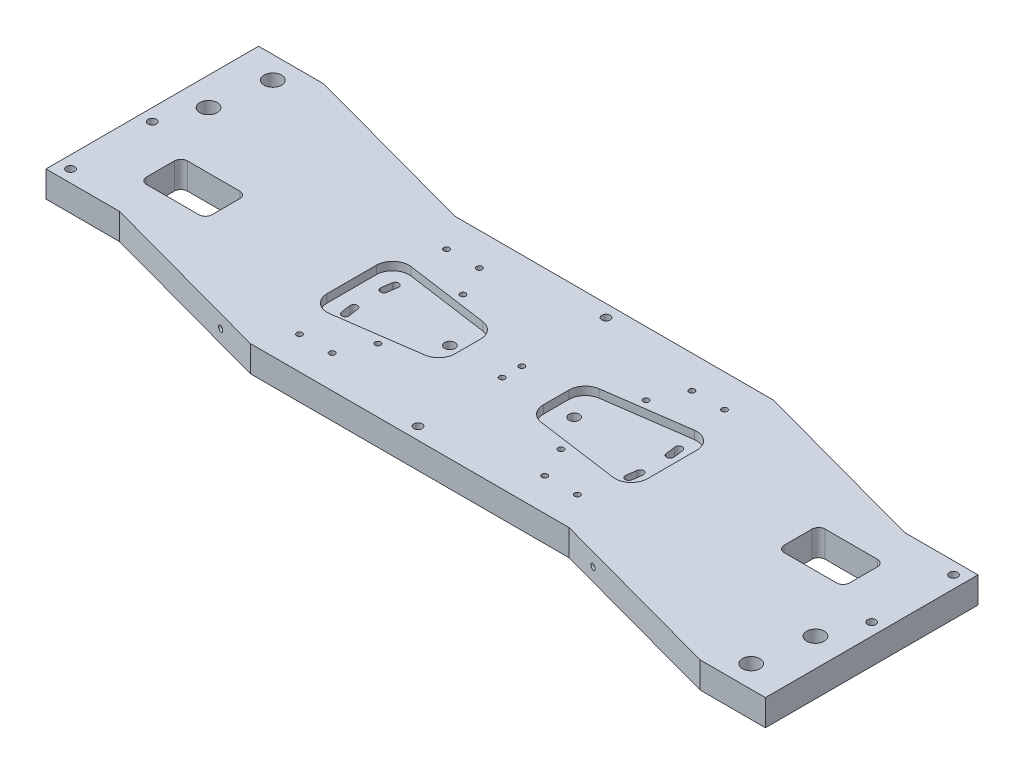
SolidWorks part; units mm, degrees
ref_plane "Front" through (0, 0, 0) normal (0, 0, 1) x (1, 0, 0)
ref_plane "Top" through (0, 0, 0) normal (0, 1, 0) x (1, 0, 0)
ref_plane "Right" through (0, 0, 0) normal (1, 0, 0) x (0, 0, -1)
sketch "Sketch1" plane through (0, 0, 0) normal (0, 0, 1) x (1, 0, 0)
  line L0 (0, 40.7324) -> (0, -22.0561) construction
  line L2 (250, 0) -> (250, -16)
  line L3 (-250, 0) -> (250, 0)
  line L4 (-250, 0) -> (-250, -16)
  line L5 (-250, -16) -> (250, -16)
  dimension "D1" = 16
  dimension "D2" = 500
  dimension "D3" = 250
extrude "Base-Extrude" add sketch "Sketch1" along normal mid plane 130
sketch "Sketch3" plane through (0, 0, 0) normal (0, 1, 0) x (-1, 0, 0)
  line L0 (-250, -65) -> (250, -65) construction
  line L1 (-210, 95) -> (-100, 65)
  line L2 (-250, 65) -> (-250, 95)
  line L3 (-250, 95) -> (-210, 95)
  line L4 (-100, 65) -> (-250, 65)
  line L5 (210, -95) -> (100, -65)
  line L6 (250, -65) -> (250, -95)
  line L7 (250, -95) -> (210, -95)
  line L8 (100, -65) -> (250, -65)
  line L9 (-250, 65) -> (250, 65) construction
  dimension "D1" = 160
  dimension "D2" = 40
  dimension "D3" = 40
  dimension "D4" = 160
  dimension "D5" = 110
  dimension "D6" = 110
extrude "Extrusion for Blade Clamping" add sketch "Sketch3" against normal up to surface (16 mm away) up to face at (0, -16, 0)
sketch "Sketch4" plane through (0, 0, 0) normal (0, 1, 0) x (-1, 0, 0)
  line L0 (-210, 95) -> (-250, 95) construction
  line L1 (-205, -35) -> (-95, -65)
  line L2 (250, 65) -> (250, 35)
  line L3 (250, 35) -> (205, 35)
  line L4 (205, 35) -> (95, 65)
  line L6 (-250, -65) -> (-250, -35)
  line L7 (-250, -35) -> (-205, -35)
  line L8 (-250, -65) -> (100, -65) construction
  line L9 (210, -95) -> (250, -95) construction
  line L10 (-100, 65) -> (250, 65) construction
  line L11 (95, 65) -> (250, 65)
  line L12 (-95, -65) -> (-250, -65)
  dimension "D1" = 130
  dimension "D2" = 45
  dimension "D3" = 130
  dimension "D4" = 45
  dimension "D5" = 110
  dimension "D6" = 110
extrude "Cutaway to Balance Blade Extrusion" cut sketch "Sketch4" against normal up to surface (16 mm away)
sketch "Sketch5" plane through (0, 0, 0) normal (0, 1, 0) x (-1, 0, 0)
  line L0 (273.4836, 0) -> (-275.6627, 0) construction
  line L1 (0, -97.6986) -> (0, 94.7931) construction
  line L2 (-215, 8.5) -> (-215, -8.5)
  line L3 (-211, -12.5) -> (-179, -12.5)
  line L4 (-175, 8.5) -> (-175, -8.5)
  line L5 (-200, -27.9658) -> (-200, 23.6075) construction
  line L6 (-211, 12.5) -> (-179, 12.5)
  line L7 (211, 12.5) -> (179, 12.5)
  line L8 (175, 8.5) -> (175, -8.5)
  line L9 (211, -12.5) -> (179, -12.5)
  line L10 (215, 8.5) -> (215, -8.5)
  arc A0 (211, -12.5) -> (215, -8.5) centre (211, -8.5) ccw
  arc A1 (175, -8.5) -> (179, -12.5) centre (179, -8.5) ccw
  arc A2 (179, 12.5) -> (175, 8.5) centre (179, 8.5) ccw
  arc A3 (215, 8.5) -> (211, 12.5) centre (211, 8.5) ccw
  arc A4 (-179, -12.5) -> (-175, -8.5) centre (-179, -8.5) ccw
  arc A5 (-215, -8.5) -> (-211, -12.5) centre (-211, -8.5) ccw
  arc A6 (-211, 12.5) -> (-215, 8.5) centre (-211, 8.5) ccw
  arc A7 (-175, 8.5) -> (-179, 12.5) centre (-179, 8.5) ccw
  point P19 (220, 0)
  point P20 (180, 0)
  point P21 (200, -12.5)
  point P22 (200, 12.5)
  point P25 (215, -12.5)
  point P28 (175, -12.5)
  point P31 (175, 12.5)
  point P34 (215, 12.5)
  point P37 (-175, -12.5)
  point P40 (-215, -12.5)
  point P43 (-215, 12.5)
  point P46 (-175, 12.5)
  dimension "D2" = 4
  dimension "D1" = 200
  dimension "D3" = 25
  dimension "D4" = 25
  dimension "D5" = 15
extrude "Holes for Wires from Blades" cut sketch "Sketch5" against normal up to surface (16 mm away)
sketch "Sketch7" plane through (0, 0, 0) normal (0, 1, 0) x (-1, 0, 0)
  line L0 (0, -90.4348) -> (0, 92.614) construction
  line L1 (264.0406, 0) -> (-271.3044, 0) construction
  line L2 (-88, -32.6979) -> (-88, 27.8372) construction
  line L3 (-27, -7.8324) -> (-27, 7.8324)
  line L5 (-98, -15) -> (-98, 15)
  line L6 (-86.6083, 24.9027) -> (-35.6083, 17.7351)
  line L8 (-86.6083, -24.9027) -> (-35.6083, -17.7351)
  line L9 (88, -31.2404) -> (88, 32.3648) construction
  line L11 (86.6083, -24.9027) -> (35.6083, -17.7351)
  line L12 (98, -15) -> (98, 15)
  line L13 (86.6083, 24.9027) -> (35.6083, 17.7351)
  line L14 (27, -7.8324) -> (27, 7.8324)
  arc A0 (86.6083, -24.9027) -> (98, -15) centre (88, -15) ccw
  arc A1 (86.6083, 24.9027) -> (98, 15) centre (88, 15) cw
  arc A2 (27, -7.8324) -> (35.6083, -17.7351) centre (37, -7.8324) ccw
  arc A3 (27, 7.8324) -> (35.6083, 17.7351) centre (37, 7.8324) cw
  arc A4 (-35.6083, 17.7351) -> (-27, 7.8324) centre (-37, 7.8324) cw
  arc A5 (-35.6083, -17.7351) -> (-27, -7.8324) centre (-37, -7.8324) ccw
  arc A6 (-98, -15) -> (-86.6083, -24.9027) centre (-88, -15) ccw
  arc A7 (-98, 15) -> (-86.6083, 24.9027) centre (-88, 15) cw
  point P22 (98, 26.5037)
  point P25 (27, -16.5253)
  point P28 (27, 16.5253)
  point P31 (-27, 16.5253)
  point P34 (-27, -16.5253)
  dimension "D12" = 10
  dimension "D2" = 88
  dimension "D3" = 71
  dimension "D4" = 8
  dimension "D5" = 30
  dimension "D6" = 88
  dimension "D7" = 71
  dimension "D8" = 8
  dimension "D9" = 30
  dimension "D10" = 8
extrude "Milling for UpperWire Pitch Adjustment" cut sketch "Sketch7" against normal blind 5
sketch "Sketch9" plane through (0, 0, 0) normal (0, 1, 0) x (-1, 0, 0)
  line L0 (0, -74.4544) -> (0, 79.539) construction
  line L1 (261.135, 0) -> (-259.6823, 0) construction
  line L2 (-86.6631, -15.281) -> (0, 0) construction
  line L3 (-87.5179, -9.1985) -> (0, 0) construction
  line L4 (0, 0) -> (-119.7635, 21.1175) construction
  line L7 (0, 0) -> (-87.5179, 9.1985) construction
  arc A0 (-88.783, -15.6548) -> (-84.5431, -14.9072) centre (-86.6631, -15.281) ccw
  circle A1 centre (38, 0) radius 3.175
  arc A2 (-84.5431, 14.9072) -> (-88.783, 15.6548) centre (-86.6631, 15.281) ccw
  arc A3 (-89.6588, 9.4235) -> (-85.3771, 8.9735) centre (-87.5179, 9.1985) ccw
  arc A4 (88.783, 15.6548) -> (89.6588, 9.4235) centre (0, 0) cw
  arc A5 (-85.3771, -8.9735) -> (-89.6588, -9.4235) centre (-87.5179, -9.1985) ccw
  arc A6 (84.5431, 14.9072) -> (85.3771, 8.9735) centre (0, 0) cw
  circle A7 centre (-38, 0) radius 3.175
  arc A8 (89.6588, 9.4235) -> (85.3771, 8.9735) centre (87.5179, 9.1985) cw
  arc A9 (84.5431, 14.9072) -> (88.783, 15.6548) centre (86.6631, 15.281) cw
  arc A10 (85.3771, -8.9735) -> (84.5431, -14.9072) centre (0, 0) cw
  arc A11 (89.6588, -9.4235) -> (88.783, -15.6548) centre (0, 0) cw
  arc A12 (-89.6588, -9.4235) -> (-88.783, -15.6548) centre (0, 0) ccw
  arc A13 (85.3771, -8.9735) -> (89.6588, -9.4235) centre (87.5179, -9.1985) cw
  arc A14 (-85.3771, -8.9735) -> (-84.5431, -14.9072) centre (0, 0) ccw
  arc A15 (88.783, -15.6548) -> (84.5431, -14.9072) centre (86.6631, -15.281) cw
  arc A16 (-86.6631, -15.281) -> (-87.5179, -9.1985) centre (0, 0) cw construction
  arc A20 (-84.5431, 14.9072) -> (-85.3771, 8.9735) centre (0, 0) ccw
  arc A21 (-88.783, 15.6548) -> (-89.6588, 9.4235) centre (0, 0) ccw
  dimension "D2" = 10
  dimension "D1" = 6.35
  dimension "D4" = 4.3053
  dimension "D5" = 88
  dimension "D10" = 10
  dimension "D3" = 6
  dimension "D8" = 38
  dimension "D11" = 6
extrude "Slots/Hole for UpperWire Pitch Adj" cut sketch "Sketch9" against normal up to surface (16 mm away) up to face at (195, -16, 0)
sketch "Sketch10" plane through (0, 0, 0) normal (0, 1, 0) x (-1, 0, 0)
  line L0 (288.9571, 0) -> (-326.217, 0) construction
  line L1 (-200, 0) -> (272.5059, -70.6165) construction
  line L2 (200, 0) -> (-295.9819, 74.125) construction
  line L3 (-233.8802, 39.8191) -> (-226.9208, 86.3855) construction
  line L4 (226.6465, -88.2209) -> (233.9439, -39.3926) construction
  line L5 (-249.4175, 37.3383) -> (-240.6968, 95.6902) construction
  line L6 (-249.4175, 37.3383) -> (-219.747, 32.904) construction
  line L7 (-219.747, 32.904) -> (-211.0263, 91.2559) construction
  line L8 (-211.0263, 91.2559) -> (-240.6968, 95.6902) construction
  line L9 (200, 0) -> (-219.747, 32.904) construction
  line L10 (-211.0263, 91.2559) -> (200, 0) construction
  point P11 (-227.6652, 81.4046)
  point P12 (-232.7786, 47.1896)
  point P15 (227.6652, -81.4046)
  point P16 (232.7786, -47.1896)
  dimension "D9" = 34.595
  dimension "D1" = 8.5
  dimension "D2" = 8.5
  dimension "D3" = 200
  dimension "D4" = 200
  dimension "D5" = 435
  dimension "D6" = 435
  dimension "D7" = 34.595
  dimension "D11" = 15
  dimension "D12" = 30
  dimension "D14" = 59
hole_wizard "#8-32 Tapped Hole1" positions "3DSketch1" profile "Sketch12" tap size "#8-32" standard "Ansi Inch" end condition through all
sketch3d "3DSketch1"
  point P0 (0, 0, 6)
  point P1 (0, 0, -6)
  dimension "D1" = 12
  dimension "D2" = 6
sketch "Sketch12" plane through (0, 0, 6) normal (1, 0, 0) x (0, 0, 1)
  line L0 (0, 0) -> (0, 16.0001)
  line L1 (0, 16.0001) -> (1.7272, 16.0001)
  line L2 (1.7272, 16.0001) -> (1.7272, 0)
  line L5 (1.7272, 0) -> (0, 0)
  line L11 (0, -6.35) -> (0, 107.95) construction
  dimension "Thru Tap Drill Dia." = 3.4544
  dimension "Thru Tap Drill Depth" = 16.0001
cosmetic thread "Cosmetic Thread1" parameters "D2"=4.1656
cosmetic thread "Cosmetic Thread2" parameters "D2"=4.1656
hole_wizard "1/4-20 Tapped Hole1" positions "Sketch14" profile "Sketch13" tap size "1/4-20" standard "Ansi Inch" end condition through all
sketch "Sketch14" plane through (0, 0, 0) normal (0, 1, 0) x (-1, 0, 0)
  line L0 (-205, -35) -> (-250, -35) construction
  line L1 (-250, 95) -> (-250, -35) construction
  line L2 (205, 35) -> (250, 35) construction
  line L3 (250, 35) -> (250, -95) construction
  point P1 (-242.5, -27.5)
  point P2 (-242.5, 22.5)
  point P3 (242.5, 27.5)
  point P4 (242.5, -22.5)
  dimension "D1" = 7.5
  dimension "D2" = 7.5
  dimension "D3" = 50
  dimension "D4" = 7.5
  dimension "D5" = 7.5
  dimension "D6" = 50
cosmetic thread "Cosmetic Thread3" parameters "D1"=12.7, "D2"=6.35
cosmetic thread "Cosmetic Thread4" parameters "D1"=12.7, "D2"=6.35
cosmetic thread "Cosmetic Thread5" parameters "D1"=12.7, "D2"=6.35
cosmetic thread "Cosmetic Thread6" parameters "D1"=12.7, "D2"=6.35
cosmetic thread "Cosmetic Thread7" parameters "D1"=12.7, "D2"=6.35
sketch "Sketch13" plane through (242.5, 0, -27.5) normal (1, 0, 0) x (0, 0, 1)
  line L0 (0, 0) -> (0, 16.0001)
  line L1 (0, 16.0001) -> (2.5527, 16.0001)
  line L2 (2.5527, 16.0001) -> (2.5527, 0)
  line L5 (2.5527, 0) -> (0, 0)
  line L11 (0, -6.35) -> (0, 107.95) construction
  dimension "Thru Tap Drill Dia." = 5.1054
  dimension "Thru Tap Drill Depth" = 16.0001
hole_wizard "#8-32 Tapped Hole2" positions "Sketch16" profile "Sketch15" tap size "#8-32" standard "Ansi Inch" end condition through all
sketch "Sketch16" plane through (0, 0, 0) normal (0, 1, 0) x (-1, 0, 0)
  line L0 (-100, 65) -> (95, 65) construction
  point P0 (-65, 45)
  point P1 (-85, 45)
  point P5 (85, 45)
  point P6 (65, 45)
  point P7 (85, -45)
  point P10 (65, -45)
  point P11 (-65, -45)
  point P12 (-85, -45)
  dimension "D1" = 15
  dimension "D2" = 20
  dimension "D3" = 20
  dimension "D4" = 20
  dimension "D5" = 10
  dimension "D6" = 20
  dimension "D7" = 10
  dimension "D8" = 20
  dimension "D9" = 15
  dimension "D10" = 20
  dimension "D11" = 20
sketch "Sketch15" plane through (65, 0, 45) normal (1, 0, 0) x (0, 0, 1)
  line L0 (0, 0) -> (0, 16.0001)
  line L1 (0, 16.0001) -> (1.7272, 16.0001)
  line L2 (1.7272, 16.0001) -> (1.7272, 0)
  line L5 (1.7272, 0) -> (0, 0)
  line L11 (0, -6.35) -> (0, 107.95) construction
  dimension "Thru Tap Drill Dia." = 3.4544
  dimension "Thru Tap Drill Depth" = 16.0001
cosmetic thread "Cosmetic Thread8" parameters "D1"=8.3312, "D2"=4.1656
cosmetic thread "Cosmetic Thread9" parameters "D1"=8.3312, "D2"=4.1656
cosmetic thread "Cosmetic Thread10" parameters "D1"=8.3312, "D2"=4.1656
cosmetic thread "Cosmetic Thread11" parameters "D1"=8.3312, "D2"=4.1656
cosmetic thread "Cosmetic Thread12" parameters "D1"=8.3312, "D2"=4.1656
cosmetic thread "Cosmetic Thread13" parameters "D1"=8.3312, "D2"=4.1656
cosmetic thread "Cosmetic Thread14" parameters "D1"=8.3312, "D2"=4.1656
cosmetic thread "Cosmetic Thread15" parameters "D1"=8.3312, "D2"=4.1656
hole_wizard "#8-32 Tapped Hole3" positions "Sketch18" profile "Sketch17" tap size "#8-32" standard "Ansi Inch" end condition through all
sketch "Sketch18" plane through (0, -16, 0) normal (0, -1, 0) x (1, 0, 0)
  line L0 (-18.3184, 0) -> (25.1902, 0) construction
  line L1 (0, 31.4329) -> (0, -35) construction
  point P0 (-56, 26)
  point P1 (56, -26)
  point P2 (56, 26)
  point P3 (-56, -26)
  dimension "D1" = 26
  dimension "D2" = 56
sketch "Sketch17" plane through (-56, -16, 26) normal (1, 0, 0) x (0, 0, -1)
  line L0 (0, 0) -> (0, 16.0001)
  line L1 (0, 16.0001) -> (1.7272, 16.0001)
  line L2 (1.7272, 16.0001) -> (1.7272, 0)
  line L5 (1.7272, 0) -> (0, 0)
  line L11 (0, -6.35) -> (0, 107.95) construction
  dimension "Thru Tap Drill Dia." = 3.4544
  dimension "Thru Tap Drill Depth" = 16.0001
cosmetic thread "Cosmetic Thread16" parameters "D1"=8.3312, "D2"=4.1656
cosmetic thread "Cosmetic Thread17" parameters "D1"=8.3312, "D2"=4.1656
cosmetic thread "Cosmetic Thread18" parameters "D1"=8.3312, "D2"=4.1656
cosmetic thread "Cosmetic Thread19" parameters "D1"=8.3312, "D2"=4.1656
hole_wizard "1/4-20 Tapped Hole2" positions "Sketch20" profile "Sketch19" tap size "1/4-20" standard "Ansi Inch" end condition through all
sketch "Sketch20" plane through (0, 0, 0) normal (0, 1, 0) x (-1, 0, 0)
  line L0 (-95, -65) -> (100, -65) construction
  line L1 (-100, 65) -> (95, 65) construction
  point P0 (0, 57.5)
  point P1 (0, -57.5)
  dimension "D1" = 7.5
  dimension "D2" = 7.5
sketch "Sketch19" plane through (0, 0, 57.5) normal (1, 0, 0) x (0, 0, 1)
  line L0 (0, 0) -> (0, 16.0001)
  line L1 (0, 16.0001) -> (2.5527, 16.0001)
  line L2 (2.5527, 16.0001) -> (2.5527, 0)
  line L5 (2.5527, 0) -> (0, 0)
  line L11 (0, -6.35) -> (0, 107.95) construction
  dimension "Thru Tap Drill Dia." = 5.1054
  dimension "Thru Tap Drill Depth" = 16.0001
cosmetic thread "Cosmetic Thread20" parameters "D2"=6.35
cosmetic thread "Cosmetic Thread21" parameters "D2"=6.35
ref_plane "Plane1" through (0, 0, 59.7) normal (0, 0, 1) x (1, 0, 0)
hole_wizard "#8-32 Tapped Hole5" positions "Sketch22" profile "Sketch21" tap size "#8-32" standard "Ansi Inch"
sketch "Sketch22" plane through (0, 0, 59.7) normal (0, 0, 1) x (1, 0, 0)
  line L0 (-250, -16) -> (-250, 0) construction
  line L1 (-95, 0) -> (-205, 0) construction
  point P0 (-120, -8)
  dimension "D1" = 130
  dimension "D2" = 8
sketch "Sketch21" plane through (-120, -8, 59.7) normal (1, 0, 0) x (0, -1, 0)
  line L0 (0, 0) -> (0, 13.3314)
  line L1 (0, 13.3314) -> (1.7272, 12.2936)
  line L2 (1.7272, 12.2936) -> (1.7272, 0)
  line L5 (1.7272, 0) -> (0, 0)
  line L10 (0, 13.3314) -> (-1.7272, 12.2936) construction
  line L11 (0, -6.35) -> (0, 107.95) construction
  dimension "Tap Drill Dia." = 3.4544
  dimension "Tap Drill Depth" = 12.2936
  dimension "Drill Angle" = 118
ref_plane "Plane2" through (0, 0, 71) normal (0, 0, 1) x (1, 0, 0)
hole_wizard "#8-32 Tapped Hole6" positions "Sketch24" profile "Sketch23" tap size "#8-32" standard "Ansi Inch"
sketch "Sketch24" plane through (0, 0, 71) normal (0, 0, 1) x (1, 0, 0)
  line L0 (100, 0) -> (210, 0) construction
  line L1 (250, -16) -> (250, 0) construction
  point P0 (120, -8)
  point P3 (250, -8)
  dimension "D1" = 8
  dimension "D2" = 130
sketch "Sketch23" plane through (120, -8, 71) normal (1, 0, 0) x (0, -1, 0)
  line L0 (0, 0) -> (0, 13.3314)
  line L1 (0, 13.3314) -> (1.7272, 12.2936)
  line L2 (1.7272, 12.2936) -> (1.7272, 0)
  line L5 (1.7272, 0) -> (0, 0)
  line L10 (0, 13.3314) -> (-1.7272, 12.2936) construction
  line L11 (0, -6.35) -> (0, 107.95) construction
  dimension "Tap Drill Dia." = 3.4544
  dimension "Tap Drill Depth" = 12.2936
  dimension "Drill Angle" = 118
ref_plane "Plane3" through (0, 0, -59.7) normal (0, 0, -1) x (-1, 0, 0)
hole_wizard "#8-32 Tapped Hole7" positions "Sketch26" profile "Sketch25" tap size "#8-32" standard "Ansi Inch"
sketch "Sketch26" plane through (0, 0, -59.7) normal (0, 0, -1) x (-1, 0, 0)
  point P0 (-120, -8)
sketch "Sketch25" plane through (120, -8, -59.7) normal (1, 0, 0) x (0, 1, 0)
  line L0 (0, 0) -> (0, 13.3314)
  line L1 (0, 13.3314) -> (1.7272, 12.2936)
  line L2 (1.7272, 12.2936) -> (1.7272, 0)
  line L5 (1.7272, 0) -> (0, 0)
  line L10 (0, 13.3314) -> (-1.7272, 12.2936) construction
  line L11 (0, -6.35) -> (0, 107.95) construction
  dimension "Tap Drill Dia." = 3.4544
  dimension "Tap Drill Depth" = 12.2936
  dimension "Drill Angle" = 118
ref_plane "Plane4" through (0, 0, -71) normal (0, 0, -1) x (-1, 0, 0)
hole_wizard "#8-32 Tapped Hole8" positions "Sketch28" profile "Sketch27" tap size "#8-32" standard "Ansi Inch"
sketch "Sketch28" plane through (0, 0, -71) normal (0, 0, -1) x (-1, 0, 0)
  point P0 (120, -8)
sketch "Sketch27" plane through (-120, -8, -71) normal (1, 0, 0) x (0, 1, 0)
  line L0 (0, 0) -> (0, 13.3314)
  line L1 (0, 13.3314) -> (1.7272, 12.2936)
  line L2 (1.7272, 12.2936) -> (1.7272, 0)
  line L5 (1.7272, 0) -> (0, 0)
  line L10 (0, 13.3314) -> (-1.7272, 12.2936) construction
  line L11 (0, -6.35) -> (0, 107.95) construction
  dimension "Tap Drill Dia." = 3.4544
  dimension "Tap Drill Depth" = 12.2936
  dimension "Drill Angle" = 118
hole_wizard "1/2-13 Tapped Hole4" positions "3DSketch3" profile "Sketch30" tap size "1/2-13" standard "Ansi Inch" end condition through all
sketch3d "3DSketch3"
  point P0 (-232.7786, 0, -47.1896)
  point P2 (-227.6652, 0, -81.4046)
  point P4 (232.7786, 0, 47.1896)
  point P6 (227.6652, 0, 81.4046)
sketch "Sketch30" plane through (-232.7786, 0, -47.1896) normal (1, 0, 0) x (0, 0, 1)
  line L0 (0, 0) -> (0, 16.0001)
  line L1 (0, 16.0001) -> (5.3581, 16.0001)
  line L2 (5.3581, 16.0001) -> (5.3581, 0)
  line L5 (5.3581, 0) -> (0, 0)
  line L11 (0, -6.35) -> (0, 107.95) construction
  dimension "Thru Tap Drill Dia." = 10.7163
  dimension "Thru Tap Drill Depth" = 16.0001
cosmetic thread "Cosmetic Thread22" parameters "D2"=12.7
cosmetic thread "Cosmetic Thread23" parameters "D2"=12.7
cosmetic thread "Cosmetic Thread24" parameters "D2"=12.7
cosmetic thread "Cosmetic Thread25" parameters "D2"=12.7
